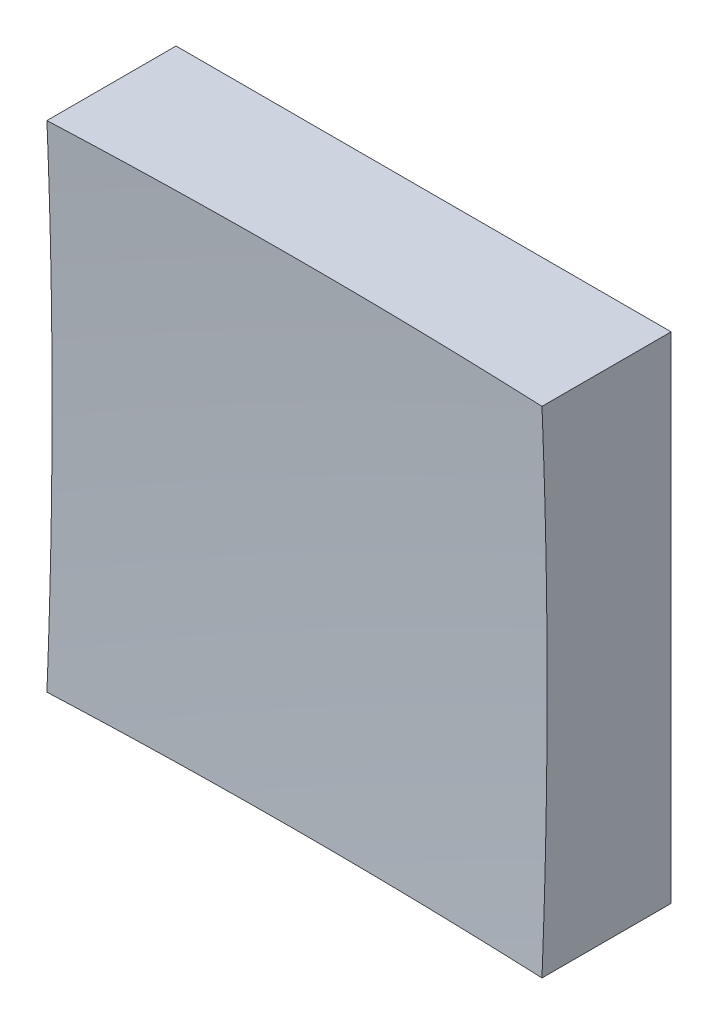
SolidWorks part; units mm, degrees
ref_plane "前视基准面" through (0, 0, 0) normal (0, 0, 1) x (1, 0, 0)
ref_plane "上视基准面" through (0, 0, 0) normal (0, 1, 0) x (1, 0, 0)
ref_plane "右视基准面" through (0, 0, 0) normal (1, 0, 0) x (0, 0, -1)
sketch "草图1" plane through (0, 0, 0) normal (0, 0, 1) x (1, 0, 0)
  line L1 (-12.5, 12.5) -> (12.5, 12.5)
  line L2 (-12.5, 12.5) -> (-12.5, -12.5)
  line L3 (-12.5, -12.5) -> (12.5, -12.5)
  line L4 (12.5, 12.5) -> (12.5, -12.5)
  line L5 (-12.5, 12.5) -> (12.5, -12.5) construction
  line L6 (-12.5, -12.5) -> (12.5, 12.5) construction
  point P0 (0, 0)
  dimension "D1" = 25
  dimension "D2" = 25
extrude "凸台-拉伸1" add sketch "草图1" along normal blind 20 contours L2 L3 L4 L1
sketch "草图2" plane through (0, 0, 0) normal (0, 1, 0) x (1, 0, 0)
  line L0 (-7.4603, -6) -> (7.3192, -6) construction
  line L1 (0, 0) -> (0, -12.1749) construction
  line L2 (292.4536, -239.1354) -> (0, -239.1354)
  line L3 (0, -239.1354) -> (0, -6)
  arc A1 (292.4536, -239.1354) -> (0, -6) centre (0, -306) ccw
  dimension "D2" = 600
  dimension "D1" = 6
revolve "切除-旋转2" cut sketch "草图2" angle 360 about L3
